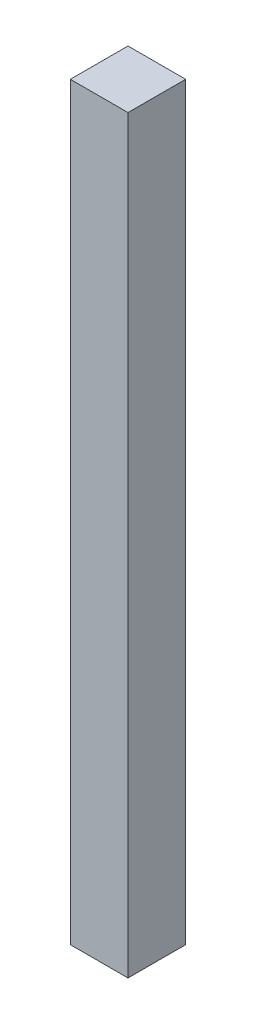
SolidWorks part; units mm, degrees
ref_plane "Alzado" through (0, 0, 0) normal (0, 0, 1) x (1, 0, 0)
ref_plane "Planta" through (0, 0, 0) normal (0, 1, 0) x (1, 0, 0)
ref_plane "Vista lateral" through (0, 0, 0) normal (1, 0, 0) x (0, 0, -1)
sketch "Croquis1" plane through (0, 0, 0) normal (0, 1, 0) x (1, 0, 0)
  line L1 (-19.05, 19.05) -> (19.05, 19.05)
  line L2 (-19.05, 19.05) -> (-19.05, -19.05)
  line L3 (-19.05, -19.05) -> (19.05, -19.05)
  line L4 (19.05, 19.05) -> (19.05, -19.05)
  line L5 (-19.05, 19.05) -> (19.05, -19.05) construction
  line L6 (-19.05, -19.05) -> (19.05, 19.05) construction
  point P0 (0, 0)
  dimension "D1" = 38.1
  dimension "D2" = 38.1
extrude "Saliente-Extruir1" add sketch "Croquis1" along normal blind 495.3
sketch "Croquis2" plane through (0, 0, 0) normal (0, -1, 0) x (1, 0, 0)
  circle A0 centre (0, 0) radius 6.35
  dimension "D1" = 12.7
extrude "Saliente-Extruir2" add sketch "Croquis2" along normal blind 12.7
ref_plane "Plano1" through (0, 0, 0) normal (1, 0, 0) x (0, 0, -1)
ref_plane "Plano2" through (0, 368.3, 0) normal (0, 1, 0) x (1, 0, 0)
ref_plane "Plano3" through (0, 127, 0) normal (0, -1, 0) x (-1, 0, 0)
